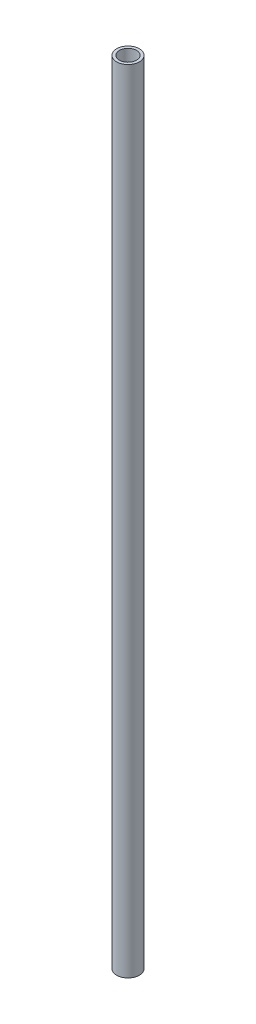
SolidWorks part; units mm, degrees
material "Copper"
ref_plane "Front Plane" through (0, 0, 0) normal (0, 0, 1) x (1, 0, 0)
ref_plane "Top Plane" through (0, 0, 0) normal (0, 1, 0) x (1, 0, 0)
ref_plane "Right Plane" through (0, 0, 0) normal (1, 0, 0) x (0, 0, -1)
sketch "Sketch1" plane through (0, 0, 0) normal (0, 1, 0) x (1, 0, 0)
  circle A0 centre (0, 0) radius 1.5
  circle A1 centre (0, 0) radius 2
  dimension "D1" = 4
  dimension "D2" = 3
extrude "Boss-Extrude1" add sketch "Sketch1" along normal mid plane 139
